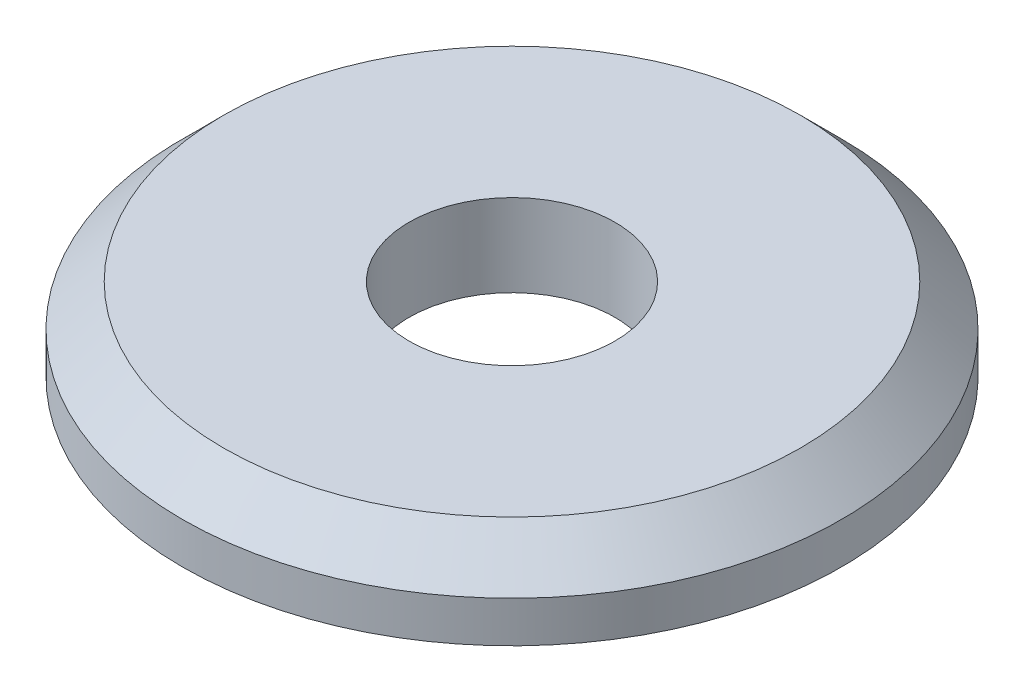
SolidWorks part; units mm, degrees
ref_plane "Front" through (0, 0, 0) normal (0, 0, 1) x (1, 0, 0)
ref_plane "Top" through (0, 0, 0) normal (0, 1, 0) x (1, 0, 0)
ref_plane "Right" through (0, 0, 0) normal (1, 0, 0) x (0, 0, -1)
sketch "Sketch1" plane through (0, 0, 0) normal (0, 1, 0) x (1, 0, 0)
  circle A0 centre (0, 0) radius 8
  dimension "D1" = 16
extrude "Boss-Extrude1" add sketch "Sketch1" along normal blind 2
chamfer "Chamfer1" distance 1 angle 45 1 edges at (0, 2, 8)
sketch "Sketch2" plane through (0, 2, 0) normal (0, 1, 0) x (1, 0, 0)
  circle A0 centre (0, 0) radius 2.5
  dimension "D1" = 5
extrude "Cut-Extrude1" cut sketch "Sketch2" against normal blind 2
